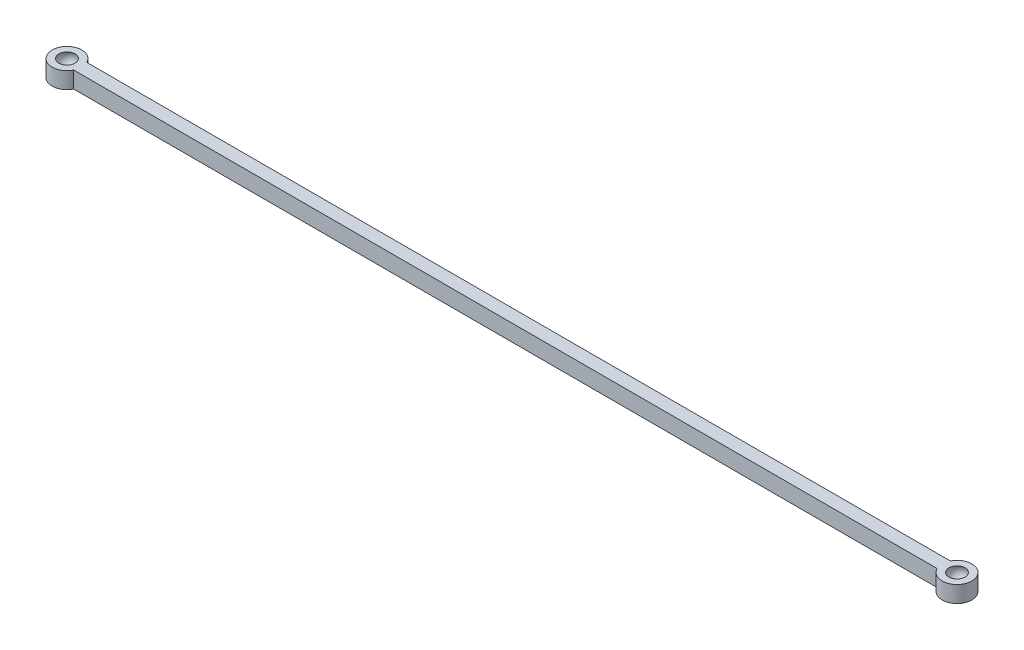
SolidWorks part; units mm, degrees
ref_plane "Front Plane" through (0, 0, 0) normal (0, 0, 1) x (1, 0, 0)
ref_plane "Top Plane" through (0, 0, 0) normal (0, 1, 0) x (1, 0, 0)
ref_plane "Right Plane" through (0, 0, 0) normal (1, 0, 0) x (0, 0, -1)
sketch "Sketch1" plane through (0, 0, 0) normal (0, 1, 0) x (1, 0, 0)
  line L1 (-135, -2) -> (135, -2)
  line L2 (-135, -2) -> (-135, 2)
  line L3 (-135, 2) -> (135, 2)
  line L4 (135, -2) -> (135, 2)
  line L5 (-135, -2) -> (135, 2) construction
  line L6 (-135, 2) -> (135, -2) construction
  circle A0 centre (135, 0) radius 4.5
  circle A1 centre (-135, 0) radius 4.5
  point P0 (0, 0)
  point P4 (0, 0)
  dimension "D2" = 9
  dimension "D1" = 270
  dimension "D3" = 4
extrude "Boss-Extrude1" add sketch "Sketch1" along normal blind 5 contours L3 A1 L1 L2 | L1 A1 L3 L2 | A1 L1 A0 L3 | L3 A0 L1 L4 | L1 A0 L3 L4
sketch3d "3DSketch1"
  line L0 (-135, 5, 0) -> (-135, 6.5, 0)
  line L1 (-135, 5, 0) -> (-135, 1, 0)
  arc A0 (-130.9689, 5, -2) -> (-130.9689, 5, 2) centre (-135, 5, 0) ccw construction
  arc A1 (-135, 1, 0) -> (-135, 6.5, 0) centre (-135, 3.75, 0) cw
  point P3 (-137.75, 3.75, 0)
  point P7 (-135, 9.5, 0)
  point P9 (0, 0, 0)
  dimension "D1" = 4
  dimension "D2" = 1.5
sketch "Sketch2" plane through (0, 5, 0) normal (0, 1, 0) x (1, 0, 0)
  circle A0 centre (-135, 0) radius 4.5
  arc A1 (-130.9689, 2) -> (-130.9689, -2) centre (-135, 0) ccw construction
sweep "Cut-Sweep1" cut profiles "3DSketch1" path "Sketch2"
mirror "Mirror1" about plane through (0, 0, 0) normal (1, 0, 0) of "Cut-Sweep1"
